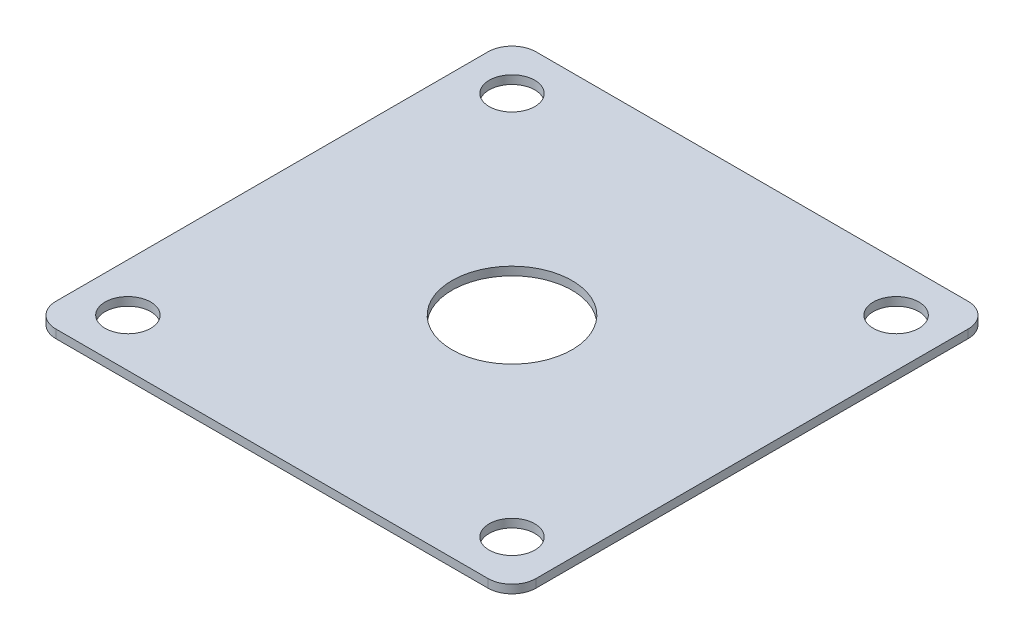
SolidWorks part; units mm, degrees
ref_plane "Front Plane" through (0, 0, 0) normal (0, 0, 1) x (1, 0, 0)
ref_plane "Top Plane" through (0, 0, 0) normal (0, 1, 0) x (1, 0, 0)
ref_plane "Right Plane" through (0, 0, 0) normal (1, 0, 0) x (0, 0, -1)
sketch "Sketch1" plane through (0, 0, 0) normal (0, 1, 0) x (1, 0, 0)
  line L0 (-37.3822, 0) -> (30.1344, 0) construction
  line L1 (-25.4, 25.4) -> (25.4, 25.4)
  line L2 (-25.4, 25.4) -> (-25.4, -25.4)
  line L3 (-25.4, -25.4) -> (25.4, -25.4)
  line L4 (25.4, 25.4) -> (25.4, -25.4)
  line L5 (0, 31.9742) -> (0, -35.223) construction
  circle A0 centre (0, 0) radius 6.35
  circle A1 centre (-20.32, 20.32) radius 2.413
  circle A5 centre (-20.32, -20.32) radius 2.413
  circle A6 centre (20.32, -20.32) radius 2.413
  circle A7 centre (20.32, 20.32) radius 2.413
  point P4 (0, 25.4)
  point P6 (25.4, 0)
  point P21 (0, 0)
  dimension "D3" = 12.7
  dimension "D6" = 4.826
  dimension "D1" = 50.8
  dimension "D2" = 50.8
  dimension "D4" = 40.64
  dimension "D5" = 40.64
extrude "Boss-Extrude1" add sketch "Sketch1" along normal blind 0.889
fillet "Fillet1" radius 2.54 4 edges at (-25.4, 0.4445, 25.4) (25.4, 0.4445, 25.4) (25.4, 0.4445, -25.4) (-25.4, 0.4445, -25.4)
